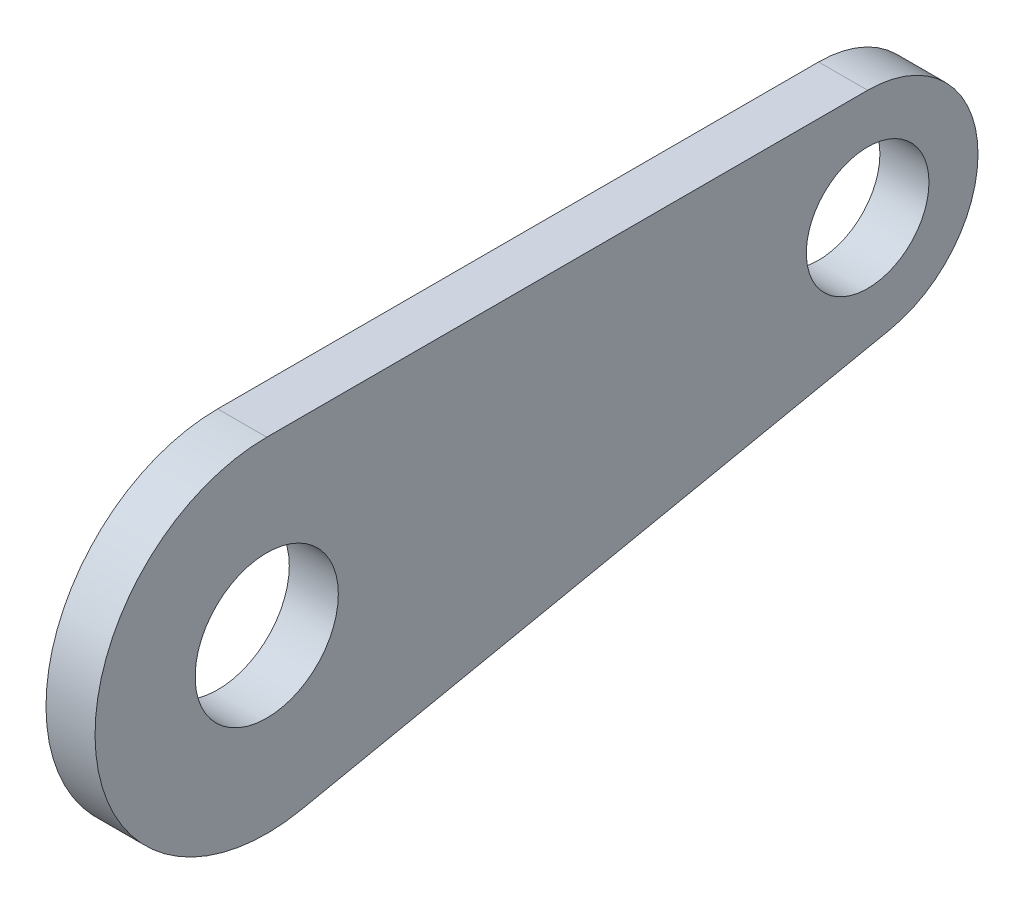
SolidWorks part; units mm, degrees
material "AISI 1035 Steel (SS)"
ref_plane "Front Plane" through (0, 0, 0) normal (0, 0, 1) x (1, 0, 0)
ref_plane "Top Plane" through (0, 0, 0) normal (0, 1, 0) x (1, 0, 0)
ref_plane "Right Plane" through (0, 0, 0) normal (1, 0, 0) x (0, 0, -1)
sketch "Sketch1" plane through (0, 0, 0) normal (1, 0, 0) x (0, 0, -1)
  line L0 (-14.4456, 5.6464) -> (5.3156, 5.6464)
  line L1 (-13.305, -5.53) -> (6.0488, -1.5381)
  arc A0 (-14.4456, 5.6464) -> (-13.305, -5.53) centre (-14.4456, 0) ccw
  arc A1 (6.0488, -1.5381) -> (5.3156, 5.6464) centre (5.3156, 2.0168) ccw
  circle A2 centre (-14.4456, 0) radius 2.3546
  circle A3 centre (5.3156, 2.0168) radius 2.0168
  dimension "D1" = 19.7612
  dimension "D2" = 2.0168
  dimension "D3" = 4.7092
extrude "Boss-Extrude1" add sketch "Sketch1" against normal blind 1.6129
